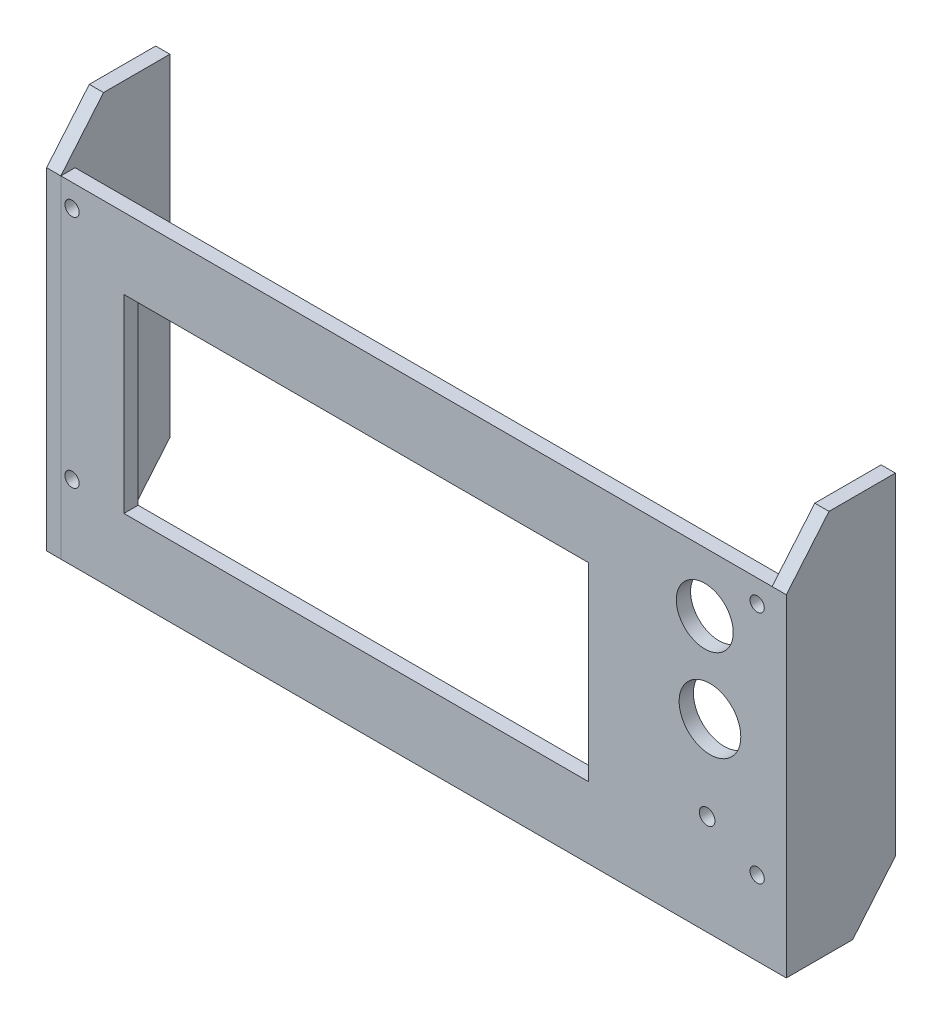
SolidWorks part; units mm, degrees
ref_plane "Alzado" through (0, 0, 0) normal (0, 0, 1) x (1, 0, 0)
ref_plane "Planta" through (0, 0, 0) normal (0, 1, 0) x (1, 0, 0)
ref_plane "Vista lateral" through (0, 0, 0) normal (1, 0, 0) x (0, 0, -1)
sketch "Croquis1" plane through (0, 0, 0) normal (0, 0, 1) x (1, 0, 0)
  line L0 (0, 0) -> (0, 70)
  line L1 (0, 70) -> (150, 70)
  line L2 (150, 70) -> (150, 0)
  line L3 (150, 0) -> (0, 0)
  circle A0 centre (135.8, 57.5) radius 6
  dimension "D1" = 70
  dimension "D2" = 150
extrude "Saliente-Extruir1" add sketch "Croquis1" along normal blind 3
sketch "Croquis2" plane through (0, 0, 3) normal (0, 0, 1) x (1, 0, 0)
  line L0 (13.3, 15) -> (13.3, 55)
  line L1 (13.3, 55) -> (111.3, 55)
  line L2 (111.3, 55) -> (111.3, 15)
  line L3 (111.3, 15) -> (13.3, 15)
  dimension "D1" = 98
  dimension "D2" = 40
  dimension "D3" = 15
  dimension "D4" = 13.3
extrude "Cortar-Extruir1" cut sketch "Croquis2" against normal blind 3
sketch "Croquis3" plane through (0, 0, 3) normal (0, 0, 1) x (1, 0, 0)
  circle A0 centre (136.9, 39.25) radius 6.5
  dimension "D1" = 13
extrude "Cortar-Extruir2" cut sketch "Croquis3" against normal through all
sketch "Croquis4" plane through (0, 0, 3) normal (0, 0, 1) x (1, 0, 0)
  circle A1 centre (136.3, 21.15) radius 1.65 construction
  circle A2 centre (136.3, 21.15) radius 1.65
extrude "Cortar-Extruir3" cut sketch "Croquis4" against normal blind 3
sketch "Croquis5" plane through (0, 0, 3) normal (0, 0, 1) x (1, 0, 0)
  circle A0 centre (146.85, 65.25) radius 1.5 construction
  circle A1 centre (146.85, 15.75) radius 1.5 construction
  circle A2 centre (2.35, 15.75) radius 1.5 construction
  circle A3 centre (2.35, 65.25) radius 1.5 construction
  circle A4 centre (146.85, 65.25) radius 1.5
  circle A5 centre (146.85, 15.75) radius 1.5
  circle A6 centre (2.35, 15.75) radius 1.5
  circle A7 centre (2.35, 65.25) radius 1.5
extrude "Cortar-Extruir4" cut sketch "Croquis5" against normal blind 3
sketch "Croquis7" plane through (150, 0, 0) normal (1, 0, 0) x (0, 0, -1)
  line L0 (-3, 70) -> (6, 80.7258)
  line L1 (6, 80.7258) -> (20, 80.7258)
  line L2 (20, 80.7258) -> (20, 10.7258)
  line L3 (20, 10.7258) -> (11, 0)
  line L4 (11, 0) -> (-3, 0)
  line L5 (-3, 70) -> (3.6334, 70) construction
  line L6 (11, 0) -> (26.1167, 0) construction
  line L7 (-3, 70) -> (-3, 0)
  dimension "D1" = 50
  dimension "D2" = 14
  dimension "D3" = 9
  dimension "D4" = 9
extrude "Saliente-Extruir4" add sketch "Croquis7" along normal blind 3
sketch "Croquis9" plane through (0, 0, 0) normal (-1, 0, 0) x (0, 0, 1)
  line L0 (3, 70) -> (3, 0) construction
  line L1 (0, 0) -> (-11, 0) construction
  line L2 (-11, 0) -> (-20, 10.7258) construction
  line L3 (-20, 10.7258) -> (-20, 80.7258) construction
  line L4 (-6, 80.7258) -> (3, 70) construction
  line L5 (3, 70) -> (3, 0)
  line L6 (0, 0) -> (-11, 0)
  line L7 (-11, 0) -> (-20, 10.7258)
  line L8 (-20, 10.7258) -> (-20, 80.7258)
  line L9 (-6, 80.7258) -> (3, 70)
  line L10 (-20, 80.7258) -> (-6, 80.7258) construction
  line L11 (-20, 80.7258) -> (-6, 80.7258)
  line M1 (0, 70) -> (0, 0)
  line M2 (0, 0) -> (3, 0)
  line M3 (3, 0) -> (3, 70)
  line M4 (3, 70) -> (0, 70)
extrude "Saliente-Extruir5" add sketch "Croquis9" along normal blind 3 separate body contours L11 L8 L7 L6 L9 M1 M4 | M4 M1 M2 M3
